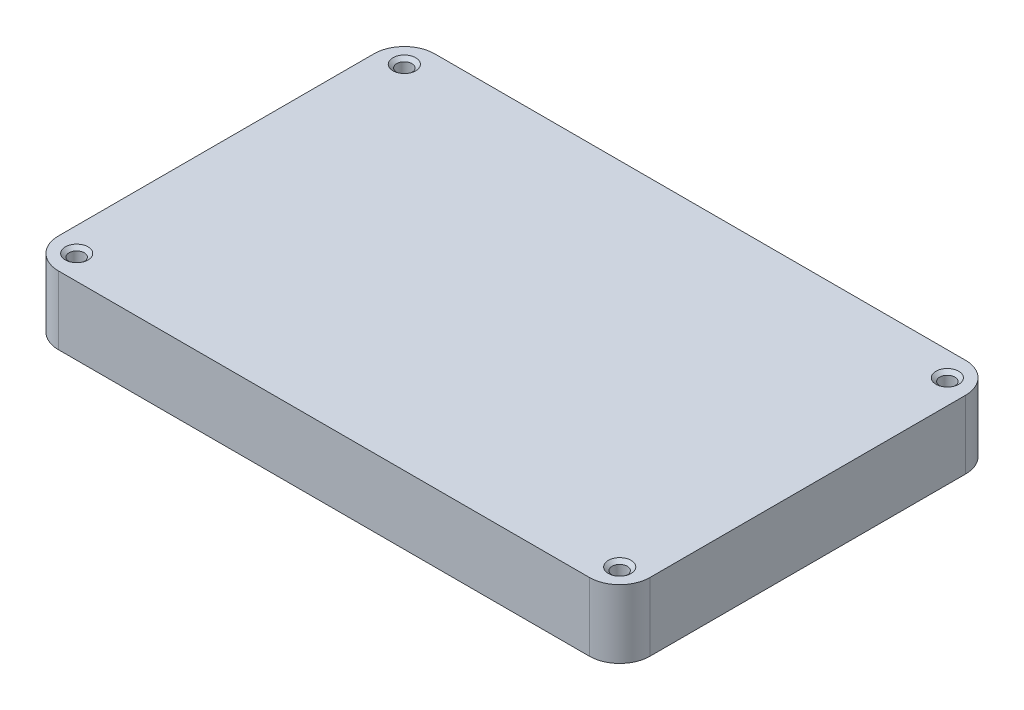
SolidWorks part; units mm, degrees
ref_plane "Front Plane" through (0, 0, 0) normal (0, 0, 1) x (1, 0, 0)
ref_plane "Top Plane" through (0, 0, 0) normal (0, 1, 0) x (1, 0, 0)
ref_plane "Right Plane" through (0, 0, 0) normal (1, 0, 0) x (0, 0, -1)
sketch "Sketch1" plane through (0, 0, 0) normal (0, 1, 0) x (1, 0, 0)
  line L1 (6.35, 0) -> (117.475, 0)
  line L2 (0, 6.35) -> (0, 72.39)
  line L3 (6.35, 78.74) -> (117.475, 78.74)
  line L4 (123.825, 6.35) -> (123.825, 72.39)
  arc A0 (117.475, 78.74) -> (123.825, 72.39) centre (117.475, 72.39) cw
  arc A1 (123.825, 6.35) -> (117.475, 0) centre (117.475, 6.35) cw
  arc A2 (6.35, 0) -> (0, 6.35) centre (6.35, 6.35) cw
  arc A3 (0, 72.39) -> (6.35, 78.74) centre (6.35, 72.39) cw
  point P11 (0, 0)
  dimension "D1" = 6.35
extrude "Boss-Extrude1" add sketch "Sketch1" along normal blind 14.2875
hole_wizard "#97 (0.0059) Diameter Hole1" positions "Sketch3" profile "Sketch4" hole size "#97" standard "ANSI Inch" end condition through all
sketch "Sketch3" plane through (0, 14.2875, 0) normal (0, 1, 0) x (1, 0, 0)
  line L0 (117.475, 78.74) -> (6.35, 78.74) construction
  line L1 (0, 72.39) -> (0, 6.35) construction
  line L2 (6.35, 0) -> (117.475, 0) construction
  line L3 (123.825, 6.35) -> (123.825, 72.39) construction
  point P0 (5.08, 5.08)
  point P1 (5.08, 73.66)
  point P3 (118.745, 73.66)
  point P5 (118.745, 5.08)
  dimension "D1" = 5.08
  dimension "D2" = 5.08
  dimension "D3" = 5.08
  dimension "D4" = 5.08
  dimension "D5" = 5.08
  dimension "D6" = 5.08
  dimension "D7" = 5.08
  dimension "D8" = 5.08
sketch "Sketch4" plane through (5.08, 14.2875, -5.08) normal (1, 0, 0) x (0, 0, 1)
  line L0 (0, 0) -> (0, 14.2875)
  line L1 (0, 14.2875) -> (1.5875, 14.2875)
  line L2 (1.5875, 14.2875) -> (1.5875, 0.666)
  line L3 (1.5875, 0.666) -> (2.3812, 0)
  line L5 (2.3812, 0) -> (0, 0)
  line L6 (-1.5875, 0.666) -> (-2.3812, 0) construction
  line L11 (0, -6.35) -> (0, 107.95) construction
  dimension "Thru Hole Dia." = 3.175
  dimension "Thru Hole Depth" = 14.2875
  dimension "Near C'Sink Dia." = 4.7625
  dimension "Near C'Sink Angle" = 100
sketch "Sketch5" plane through (0, 0, 0) normal (0, -1, 0) x (-1, 0, 0)
  line L0 (0, 72.39) -> (0, 6.35) construction
  line L3 (-6.35, 0) -> (-117.475, 0) construction
  line L6 (-111.125, 73.1838) -> (-111.125, 62.865)
  line L7 (-12.7, 73.1838) -> (-12.7, 59.055)
  line L8 (-10.16, 56.515) -> (-5.5563, 56.515)
  line L9 (-117.475, 56.515) -> (-118.2687, 56.515)
  line L12 (-5.5562, 22.225) -> (-5.5563, 56.515)
  line L13 (-12.7, 15.875) -> (-12.7, 5.5562)
  line L14 (-111.125, 5.5562) -> (-12.7, 5.5562)
  line L15 (-111.125, 73.1838) -> (-12.7, 73.1838)
  line L17 (-118.2687, 56.515) -> (-118.2687, 12.7)
  line L18 (-118.2687, 12.7) -> (-117.475, 12.7)
  line L19 (-111.125, 6.35) -> (-111.125, 5.5562)
  line L20 (-6.35, 22.225) -> (-5.5562, 22.225)
  line L21 (-123.825, 6.35) -> (-123.825, 72.39) construction
  line L22 (-117.475, 78.74) -> (-6.35, 78.74) construction
  arc A0 (-111.125, 62.865) -> (-117.475, 56.515) centre (-117.475, 62.865) cw
  arc A1 (-6.35, 22.225) -> (-12.7, 15.875) centre (-6.35, 15.875) ccw
  arc A2 (-117.475, 12.7) -> (-111.125, 6.35) centre (-117.475, 6.35) cw
  arc A3 (-12.7, 59.055) -> (-10.16, 56.515) centre (-10.16, 59.055) ccw
  point P8 (-7.8581, 56.515)
  point P9 (-111.125, 5.9531)
  dimension "D13" = 6.35
  dimension "D14" = 6.35
  dimension "D15" = 2.54
  dimension "D1" = 12.7
  dimension "D2" = 12.7
  dimension "D3" = 5.5562
  dimension "D4" = 5.5562
  dimension "D5" = 5.5562
  dimension "D6" = 12.7
  dimension "D7" = 5.5562
  dimension "D8" = 22.225
  dimension "D9" = 22.225
  dimension "D10" = 22.225
  dimension "D11" = 12.7
  dimension "D12" = 12.7
extrude "Cut-Extrude1" cut sketch "Sketch5" against normal blind 12.065
